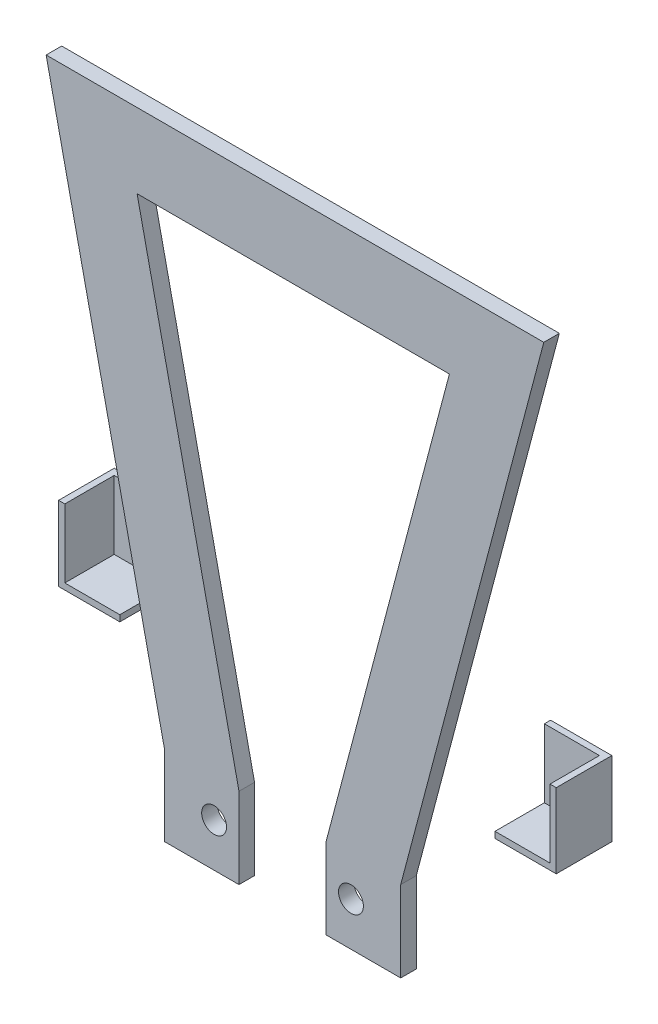
SolidWorks part; units mm, degrees
ref_plane "Plano frontal" through (0, 0, 0) normal (0, 0, 1) x (1, 0, 0)
ref_plane "Plano superior" through (0, 0, 0) normal (0, 1, 0) x (1, 0, 0)
ref_plane "Plano direito" through (0, 0, 0) normal (1, 0, 0) x (0, 0, -1)
ref_plane "Plano1" through (0, 0, -2.5) normal (0, 0, -1) x (-1, 0, 0)
sketch "Esboço1" plane through (0, 0, -2.5) normal (0, 0, -1) x (-1, 0, 0)
  line L0 (-17, -54) -> (-17, -67)
  line L1 (-17, -67) -> (21, -67)
  line L2 (21, -67) -> (21, -54)
  line L3 (21, -54) -> (40, 33)
  line L4 (40, 33) -> (-40, 33)
  line L5 (-40, 33) -> (-17, -54)
extrude "Ressalto-extrusão1" add sketch "Esboço1" against normal blind 2.5
sketch "Esboço2" plane through (0, 0, 0) normal (0, 0, 1) x (1, 0, 0)
  line L0 (-9, -67) -> (5, -67)
  line L1 (5, -67) -> (5, -54)
  line L2 (5, -54) -> (24.8276, 21)
  line L3 (24.8276, 21) -> (-25.3793, 21)
  line L4 (-25.3793, 21) -> (-9, -54)
  line L5 (-9, -54) -> (-9, -67)
extrude "Corte-extrusão1" cut sketch "Esboço2" against normal through all
ref_plane "Plano2" through (0, -34.4981, 0) normal (0, 1, 0) x (1, 0, 0)
sketch "Esboço3" plane through (0, -34.4981, 0) normal (0, 1, 0) x (1, 0, 0)
  line L0 (-16.9036, 17.5) -> (-18.9518, 17.5)
  line L1 (-18.9518, 17.5) -> (-18.9518, 2.5)
  line L2 (-18.9518, 2.5) -> (-16.9036, 2.5)
  line L3 (-16.9036, 2.5) -> (-16.9036, 17.5)
  line L4 (-18.9518, 17.5) -> (-18.9518, 2.5) construction
revolve "Revolução1" [suppressed] add sketch "Esboço3" angle 360 about L4
ref_plane "Plano3" through (0, -32.7834, 0) normal (0, 1, 0) x (1, 0, 0)
sketch "Esboço4" plane through (0, -32.7834, 0) normal (0, 1, 0) x (1, 0, 0)
  line L0 (18.8748, 17.5) -> (17, 17.5)
  line L1 (17, 17.5) -> (17, 2.5)
  line L2 (17, 2.5) -> (18.8748, 2.5)
  line L3 (18.8748, 2.5) -> (18.8748, 17.5)
  line L4 (17, 17.5) -> (17, 2.5) construction
revolve "Revolução2" [suppressed] add sketch "Esboço4" angle 360 about L4
hole_wizard "Furo de diâmetro Ø4.0 (4)1" positions "Esboço6" profile "Esboço5" hole size "Ø4.0" standard "Ansi Metric"
sketch "Esboço6" plane through (0, 0, 0) normal (0, 0, 1) x (1, 0, 0)
  point P0 (-13, -60)
  point P1 (9, -60)
sketch "Esboço5" plane through (-13, -60, 0) normal (1, 0, 0) x (0, -1, 0)
  line L0 (0, 0) -> (0, 2.5)
  line L1 (0, 2.5) -> (2, 2.5)
  line L2 (2, 2.5) -> (2, 0)
  line L5 (2, 0) -> (0, 0)
  line L11 (0, -6.35) -> (0, 107.95) construction
  dimension "Thru Hole Dia." = 4
  dimension "Thru Hole Depth" = 2.5
ref_plane "Plano4" through (0, -42, 0) normal (0, -1, 0) x (-1, 0, 0)
sketch "Esboço7" plane through (0, -42, 0) normal (0, 1, 0) x (1, 0, 0)
  line L0 (0, -1.375) -> (0, 1.375) construction
  line L1 (40, 2) -> (30.1534, 2)
  line L2 (40, 2) -> (40, 10.9421)
  line L3 (40, 10.9421) -> (30.1534, 10.9421)
  line L4 (30.1534, 2) -> (30.1534, 10.9421)
  line L5 (-37.8632, 6.9566) -> (-48.9876, 6.9566)
  line L6 (-37.8632, 6.9566) -> (-37.8632, 17.2701)
  line L7 (-37.8632, 17.2701) -> (-48.9876, 17.2701)
  line L8 (-48.9876, 6.9566) -> (-48.9876, 17.2701)
  line L9 (17, 0) -> (5, 0) construction
  dimension "D1" = 40
  dimension "D2" = 2
extrude "Ressalto-extrusão2" add sketch "Esboço7" along normal blind 12 separate body contours L1 L4 L3 L2
shell "Casca1" thickness 1
mirror "Espelhar3" about plane through (0, 0, 0) normal (1, 0, 0) of bodies 108
